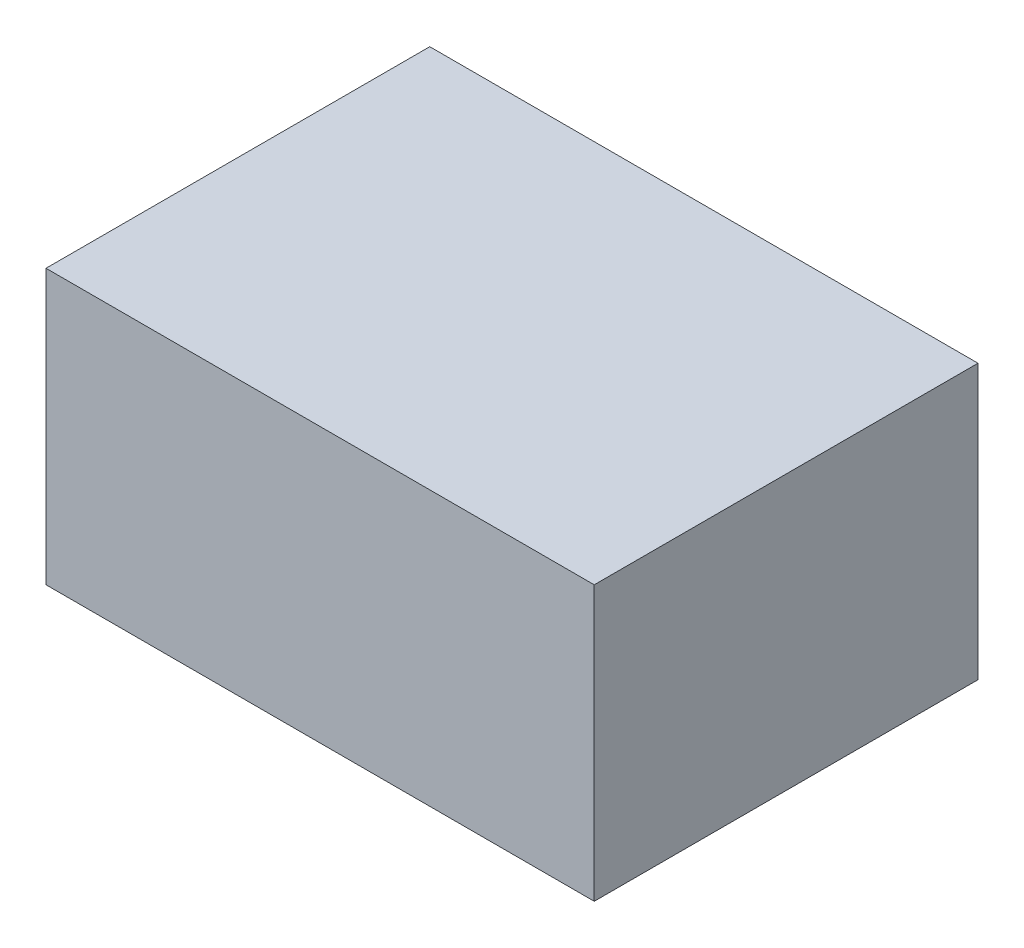
SolidWorks part; units mm, degrees
ref_plane "Front Plane" through (0, 0, 0) normal (0, 0, 1) x (1, 0, 0)
ref_plane "Top Plane" through (0, 0, 0) normal (0, 1, 0) x (1, 0, 0)
ref_plane "Right Plane" through (0, 0, 0) normal (1, 0, 0) x (0, 0, -1)
sketch "Sketch2" plane through (0, 0, 0) normal (0, 1, 0) x (1, 0, 0)
  line L1 (50, 35) -> (-50, 35)
  line L2 (50, 35) -> (50, -35)
  line L3 (50, -35) -> (-50, -35)
  line L4 (-50, 35) -> (-50, -35)
  line L5 (50, 35) -> (-50, -35) construction
  line L6 (50, -35) -> (-50, 35) construction
  point P0 (0, 0)
  dimension "D1" = 100
  dimension "D2" = 70
extrude "Boss-Extrude1" add sketch "Sketch2" along normal blind 50
